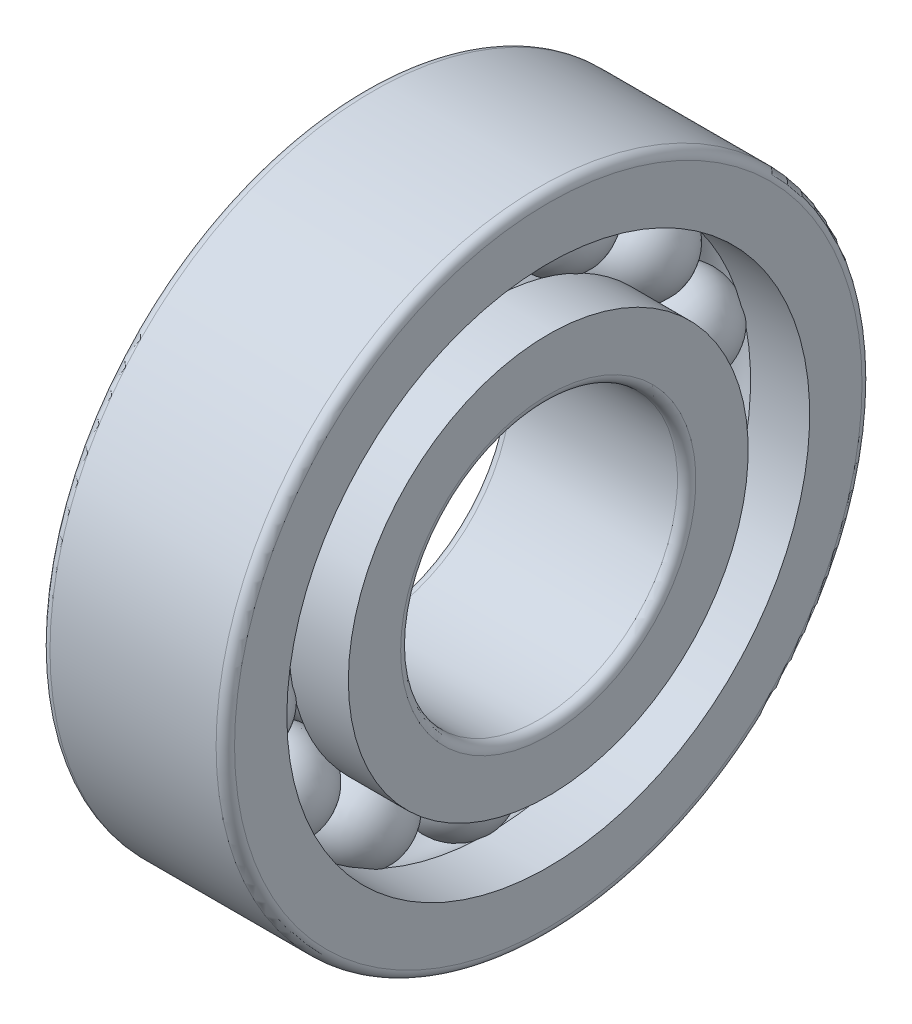
SolidWorks part; units mm, degrees
ref_plane "Front" through (0, 0, 0) normal (0, 0, 1) x (1, 0, 0)
ref_plane "Top" through (0, 0, 0) normal (0, 1, 0) x (1, 0, 0)
ref_plane "Right" through (0, 0, 0) normal (1, 0, 0) x (0, 0, -1)
sketch "Sketch1" plane through (0, 0, 0) normal (0, 0, 1) x (1, 0, 0)
  line L0 (-9.6833, 0) -> (9.8371, 0) construction
  line L1 (-0.5, 2.5) -> (0.5, 2.5)
  line L2 (-4.5966, 2.5) -> (4.6657, 2.5) construction
  arc A0 (0.5, 2.5) -> (-0.5, 2.5) centre (0, 2.5) ccw
  dimension "dia" = 1
  dimension "d0" = 5
revolve "Revolve1" add sketch "Sketch1" angle 360 about L2
sketch "Sketch2" plane through (0, 0, 0) normal (0, 0, 1) x (1, 0, 0)
  line L0 (-1, 2.1667) -> (-1, 1.5)
  line L1 (-1, 1.5) -> (1, 1.5)
  line L2 (1, 1.5) -> (1, 2.1667)
  line L3 (1, 2.1667) -> (0.3592, 2.1667)
  line L4 (-6.9714, 0) -> (8.1665, 0) construction
  line L5 (-6.7058, 2.5) -> (6.7058, 2.5) construction
  line L6 (-0.3592, 2.1667) -> (-1, 2.1667)
  arc A0 (-0.3592, 2.1667) -> (0.3592, 2.1667) centre (0, 2.5) ccw
  dimension "D5" = 0.98
  dimension "B" = 2
  dimension "B/2" = 1
  dimension "D3" = 2.5
  dimension "d" = 3
  dimension "D4" = 0.6667
revolve "Revolve2" add sketch "Sketch2" angle 360 about L4
sketch "Sketch3" plane through (0, 0, 0) normal (0, 0, 1) x (1, 0, 0)
  line L0 (-8.7107, 0) -> (9.1288, 0) construction
  line L1 (-1, 3.5) -> (1, 3.5)
  line L2 (-1, 3.5) -> (-1, 2.8333)
  line L3 (-1, 2.8333) -> (-0.3592, 2.8333)
  line L4 (1, 3.5) -> (1, 2.8333)
  line L5 (-7.2948, 2.5) -> (7.2948, 2.5) construction
  line L6 (0.3592, 2.8333) -> (1, 2.8333)
  arc A0 (0.3592, 2.8333) -> (-0.3592, 2.8333) centre (0, 2.5) ccw
  dimension "D1" = 0.98
  dimension "DD" = 7
  dimension "B" = 2
  dimension "B/2" = 1
  dimension "D4" = 2.5
  dimension "D5" = 0.6667
revolve "Revolve3" add sketch "Sketch3" angle 360 about L0
pattern_circular "Circular-Pattern1" count 14 over 360 about axis through (0, 0, 0) along (1, 0, 0) of "Revolve1"
fillet "Fillet1" radius 0.1 4 edges at (-1, 0, 1.5) (-1, 0, 3.5) (1, 0, 3.5) (1, 0, 1.5)
equation "\"d0@Sketch1\" = ( \"DD@Sketch3\" + \"d@Sketch2\" )  / 2"
equation "\"dia@Sketch1\" =  ( \"DD@Sketch3\" - \"d@Sketch2\" )  / 4"
equation "\"D3@Sketch2\" = ( \"DD@Sketch3\" + \"d@Sketch2\" )  / 2 / 2"
equation "\"D4@Sketch2\" = ( \"DD@Sketch3\" - \"d@Sketch2\" )  / 6"
equation "\"D5@Sketch2\" = \"dia@Sketch1\" - 0.02"
equation "\"B/2@Sketch2\" = \"B@Sketch2\" / 2"
equation "\"D4@Sketch3\" = ( \"DD@Sketch3\" + \"d@Sketch2\" )  / 2 / 2"
equation "\"D5@Sketch3\" = ( \"DD@Sketch3\" - \"d@Sketch2\" )  / 6"
equation "\"B@Sketch3\" = \"B@Sketch2\""
equation "\"B/2@Sketch3\" = \"B@Sketch3\" / 2"
equation "\"D1@Sketch3\" = \"dia@Sketch1\" - 0.02"
equation "\"m@Circular-Pattern1\" = int( 3.14159265 / atn(( \"dia@Sketch1\" / 2) / sqr(( \"DD@Sketch3\" + \"d@Sketch2\" )  / 2 * ( \"DD@Sketch3\" + \"d@Sketch2\" )  / 2/4 - ( \"dia@Sketch1\" / 2) *  ( \"dia@Sketch1\" / 2))))-1"
